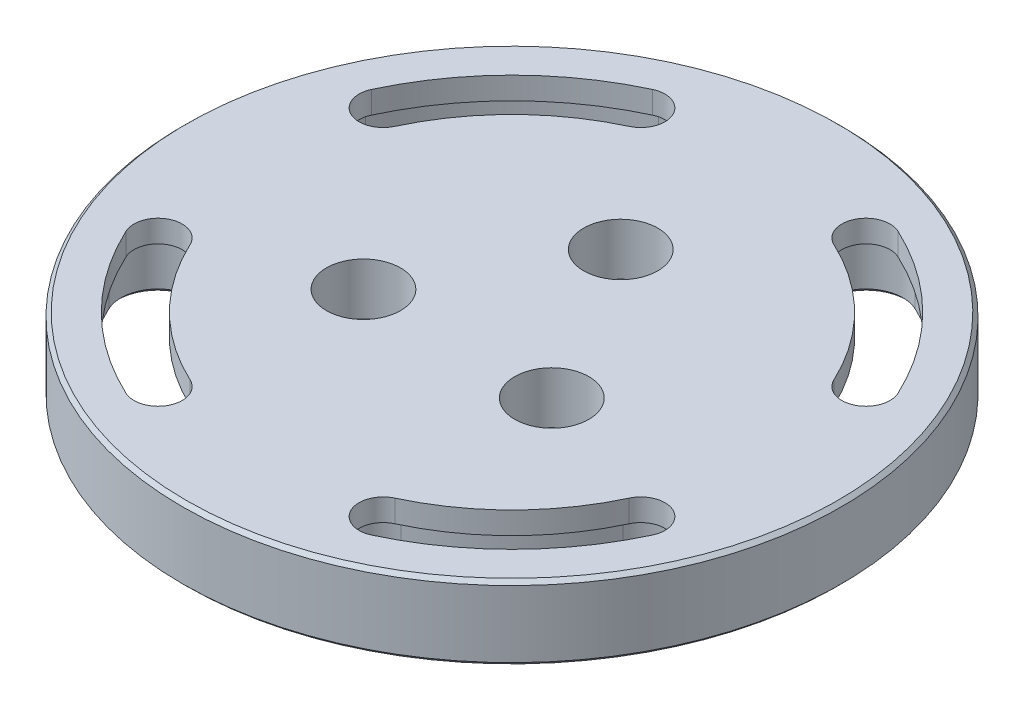
SolidWorks part; units mm, degrees
ref_plane "Front Plane" through (0, 0, 0) normal (0, 0, 1) x (1, 0, 0)
ref_plane "Top Plane" through (0, 0, 0) normal (0, 1, 0) x (1, 0, 0)
ref_plane "Right Plane" through (0, 0, 0) normal (1, 0, 0) x (0, 0, -1)
sketch "Sketch1" plane through (0, 0, 0) normal (0, 1, 0) x (1, 0, 0)
  line L0 (0, 0) -> (44.45, 0)
  line L1 (15.1809, 32.5555) -> (0, 0)
  line L2 (-25.4, -25.4) -> (25.4, -25.4)
  line L3 (-25.4, -25.4) -> (-25.4, 25.4)
  line L4 (-25.4, 25.4) -> (25.4, 25.4)
  line L5 (25.4, -25.4) -> (25.4, 25.4)
  line L6 (-25.4, -25.4) -> (25.4, 25.4) construction
  line L7 (-25.4, 25.4) -> (25.4, -25.4) construction
  line L8 (32.5555, 15.1809) -> (0, 0)
  circle A0 centre (0, 0) radius 44.45
  circle A1 centre (0, 0) radius 35.921
  arc A2 (15.1809, 32.5555) -> (32.5555, 15.1809) centre (0, 0) cw construction
  arc A3 (37.087, 17.294) -> (17.294, 37.087) centre (0, 0) ccw
  arc A4 (28.024, 13.0678) -> (13.0678, 28.024) centre (0, 0) ccw
  arc A5 (28.024, 13.0678) -> (37.087, 17.294) centre (32.5555, 15.1809) ccw
  arc A6 (17.294, 37.087) -> (13.0678, 28.024) centre (15.1809, 32.5555) ccw
  arc A7 (32.5555, -15.1809) -> (15.1809, -32.5555) centre (0, 0) cw construction
  arc A8 (17.294, -37.087) -> (37.087, -17.294) centre (0, 0) ccw
  arc A9 (13.0678, -28.024) -> (28.024, -13.0678) centre (0, 0) ccw
  arc A10 (13.0678, -28.024) -> (17.294, -37.087) centre (15.1809, -32.5555) ccw
  arc A11 (37.087, -17.294) -> (28.024, -13.0678) centre (32.5555, -15.1809) ccw
  arc A12 (-15.1809, -32.5555) -> (-32.5555, -15.1809) centre (0, 0) cw construction
  arc A13 (-37.087, -17.294) -> (-17.294, -37.087) centre (0, 0) ccw
  arc A14 (-28.024, -13.0678) -> (-13.0678, -28.024) centre (0, 0) ccw
  arc A15 (-28.024, -13.0678) -> (-37.087, -17.294) centre (-32.5555, -15.1809) ccw
  arc A16 (-17.294, -37.087) -> (-13.0678, -28.024) centre (-15.1809, -32.5555) ccw
  arc A17 (-32.5555, 15.1809) -> (-15.1809, 32.5555) centre (0, 0) cw construction
  arc A18 (-17.294, 37.087) -> (-37.087, 17.294) centre (0, 0) ccw
  arc A19 (-13.0678, 28.024) -> (-28.024, 13.0678) centre (0, 0) ccw
  arc A20 (-13.0678, 28.024) -> (-17.294, 37.087) centre (-15.1809, 32.5555) ccw
  arc A21 (-37.087, 17.294) -> (-28.024, 13.0678) centre (-32.5555, 15.1809) ccw
  point P11 (25.4, 25.4)
  point P24 (25.4, -25.4)
  point P31 (-25.4, -25.4)
  point P38 (-25.4, 25.4)
  point P43 (0, 0)
  dimension "D1" = 88.9
  dimension "D2" = 50.8
  dimension "D6" = 5
  dimension "D3" = 50.8
  dimension "D4" = 20
  dimension "D5" = 20
  dimension "D7" = 4
extrude "Boss-Extrude1" add sketch "Sketch1" along normal blind 10
sketch "Sketch2" plane through (0, 10, 0) normal (0, 1, 0) x (1, 0, 0)
  arc A0 (-13.8074, 29.61) -> (-16.5544, 35.501) centre (-15.1809, 32.5555) ccw
  arc A1 (-37.087, 17.294) -> (-28.024, 13.0678) centre (-32.5555, 15.1809) ccw construction
  circle A2 centre (0, 0) radius 44.45
  circle A3 centre (0, 0) radius 44.45
  arc A4 (-17.294, 37.087) -> (-37.087, 17.294) centre (0, 0) ccw construction
  arc A5 (-13.0678, 28.024) -> (-17.294, 37.087) centre (-15.1809, 32.5555) ccw construction
  arc A6 (-13.0678, 28.024) -> (-28.024, 13.0678) centre (0, 0) ccw construction
  arc A7 (-37.087, 17.294) -> (-28.024, 13.0678) centre (-32.5555, 15.1809) ccw
  arc A8 (-17.294, 37.087) -> (-37.087, 17.294) centre (0, 0) ccw
  arc A9 (-13.0678, 28.024) -> (-17.294, 37.087) centre (-15.1809, 32.5555) ccw
  arc A10 (-13.0678, 28.024) -> (-28.024, 13.0678) centre (0, 0) ccw
  arc A11 (-16.5544, 35.501) -> (-35.501, 16.5544) centre (0, 0) ccw
  arc A12 (-35.501, 16.5544) -> (-29.61, 13.8074) centre (-32.5555, 15.1809) ccw
  arc A13 (-13.8074, 29.61) -> (-29.61, 13.8074) centre (0, 0) ccw
  arc A14 (29.61, 13.8074) -> (13.8074, 29.61) centre (0, 0) ccw
  arc A15 (29.61, 13.8074) -> (35.501, 16.5544) centre (32.5555, 15.1809) ccw
  arc A16 (35.501, 16.5544) -> (16.5544, 35.501) centre (0, 0) ccw
  arc A17 (16.5544, 35.501) -> (13.8074, 29.61) centre (15.1809, 32.5555) ccw
  arc A18 (13.8074, -29.61) -> (29.61, -13.8074) centre (0, 0) ccw
  arc A19 (13.8074, -29.61) -> (16.5544, -35.501) centre (15.1809, -32.5555) ccw
  arc A20 (16.5544, -35.501) -> (35.501, -16.5544) centre (0, 0) ccw
  arc A21 (35.501, -16.5544) -> (29.61, -13.8074) centre (32.5555, -15.1809) ccw
  arc A22 (-29.61, -13.8074) -> (-13.8074, -29.61) centre (0, 0) ccw
  arc A23 (-29.61, -13.8074) -> (-35.501, -16.5544) centre (-32.5555, -15.1809) ccw
  arc A24 (-35.501, -16.5544) -> (-16.5544, -35.501) centre (0, 0) ccw
  arc A25 (-16.5544, -35.501) -> (-13.8074, -29.61) centre (-15.1809, -32.5555) ccw
  point P40 (0, 0)
  arc M2 (28.024, 13.0678) -> (13.0678, 28.024) centre (0, 0) ccw
  arc M3 (13.0678, 28.024) -> (17.294, 37.087) centre (15.1809, 32.5555) cw
  arc M4 (17.294, 37.087) -> (37.087, 17.294) centre (0, 0) cw
  arc M5 (37.087, 17.294) -> (28.024, 13.0678) centre (32.5555, 15.1809) cw
  arc M6 (-17.294, 37.087) -> (-13.0678, 28.024) centre (-15.1809, 32.5555) cw
  arc M7 (-13.0678, 28.024) -> (-28.024, 13.0678) centre (0, 0) ccw
  arc M8 (-28.024, 13.0678) -> (-37.087, 17.294) centre (-32.5555, 15.1809) cw
  arc M9 (-37.087, 17.294) -> (-17.294, 37.087) centre (0, 0) cw
  arc M10 (13.0678, -28.024) -> (28.024, -13.0678) centre (0, 0) ccw
  arc M11 (28.024, -13.0678) -> (37.087, -17.294) centre (32.5555, -15.1809) cw
  arc M12 (37.087, -17.294) -> (17.294, -37.087) centre (0, 0) cw
  arc M13 (17.294, -37.087) -> (13.0678, -28.024) centre (15.1809, -32.5555) cw
  arc M15 (-28.024, -13.0678) -> (-13.0678, -28.024) centre (0, 0) ccw
  arc M16 (-13.0678, -28.024) -> (-17.294, -37.087) centre (-15.1809, -32.5555) cw
  arc M17 (-17.294, -37.087) -> (-37.087, -17.294) centre (0, 0) cw
  arc M18 (-37.087, -17.294) -> (-28.024, -13.0678) centre (-32.5555, -15.1809) cw
  dimension "D1" = 0
  dimension "D2" = 1.75
  dimension "D3" = 4
extrude "Boss-Extrude2" add sketch "Sketch2" against normal blind 3 contours A0 A13 A12 A11 M6 M9 M8 M7 | A17 A16 A15 A14 M2 M5 M4 M3 | A21 A20 A19 A18 M10 M13 M12 M11 | A25 A24 A23 A22 M15 M18 M17 M16 | A9 A8 A7 A10
sketch "Sketch3" plane through (0, 10, 0) normal (0, 1, 0) x (1, 0, 0)
  line L1 (-12.7, -7.3323) -> (12.7, -7.3323)
  line L2 (12.7, -7.3323) -> (0, 14.6647)
  line L3 (0, 14.6647) -> (-12.7, -7.3323)
  circle A0 centre (0, 0) radius 14.6647
  circle A1 centre (0, 0) radius 44.45
  circle A2 centre (0, 0) radius 44.45
  circle A3 centre (0, 14.6647) radius 5
  circle A4 centre (-12.7, -7.3323) radius 5
  circle A5 centre (12.7, -7.3323) radius 5
  dimension "D5" = 10
  dimension "D6" = 10
  dimension "D7" = 10
  dimension "D2" = 60
  dimension "D3" = 25.4
  dimension "D4" = 60
  dimension "D1" = 0
extrude "Cut-Extrude1" cut sketch "Sketch3" against normal blind 10 contours A0 A3 | L2 A3 A0 | L3 A3 L2 | A0 A3 L3 | L3 A4 A0 | L1 A4 L3 | A0 A4 L1 | A0 A4 | L1 A5 A0 | L2 A5 L1 | A0 A5 L2 | A0 A5
sketch "Sketch4" plane through (0, 0, 0) normal (0, 1, 0) x (1, 0, 0)
  circle A0 centre (12.7, -7.3323) radius 5 construction
  circle A1 centre (-12.7, -7.3323) radius 5 construction
  circle A2 centre (0, 14.6647) radius 5 construction
  circle A3 centre (12.7, -7.3323) radius 5
  circle A4 centre (-12.7, -7.3323) radius 5
  circle A5 centre (0, 14.6647) radius 5
  circle A6 centre (0, 14.6647) radius 3.25
  circle A7 centre (-12.7, -7.3323) radius 3.25
  circle A8 centre (12.7, -7.3323) radius 3.25
  dimension "D1" = 1.75
extrude "Boss-Extrude4" add sketch "Sketch4" along normal blind 3
chamfer "Chamfer1" distance 0.5 angle 45 18 edges at (28.9355, 0, 28.9355) (10.6493, 0, 34.6686) (21.8645, 0, 21.8645) (34.6686, 0, 10.6493) (-10.6493, 0, 34.6686) (-21.8645, 0, 21.8645) (-28.9355, 0, 28.9355) (-34.6686, 0, 10.6493) (-34.6686, 0, -10.6493) (-28.9355, 0, -28.9355) (-10.6493, 0, -34.6686) (-21.8645, 0, -21.8645) (21.8645, 0, -21.8645) (10.6493, 0, -34.6686) (28.9355, 0, -28.9355) (34.6686, 0, -10.6493) (0, 10, 44.45) (0, 0, 44.45)
